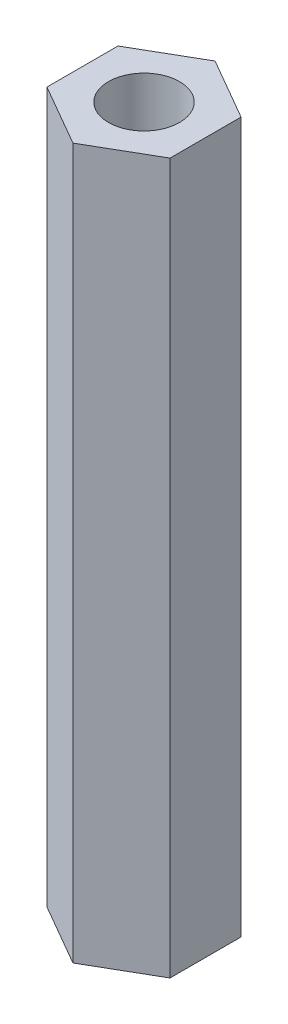
SolidWorks part; units mm, degrees
ref_plane "Front Plane" through (0, 0, 0) normal (0, 0, 1) x (1, 0, 0)
ref_plane "Top Plane" through (0, 0, 0) normal (0, 1, 0) x (1, 0, 0)
ref_plane "Right Plane" through (0, 0, 0) normal (1, 0, 0) x (0, 0, -1)
sketch "Sketch1" plane through (0, 0, 0) normal (0, 1, 0) x (1, 0, 0)
  line L0 (0, 0) -> (2.6, 0) construction
  line L1 (0, 3.0022) -> (-2.6, 1.5011)
  line L2 (-2.6, 1.5011) -> (-2.6, -1.5011)
  line L3 (-2.6, -1.5011) -> (0, -3.0022)
  line L4 (0, -3.0022) -> (2.6, -1.5011)
  line L5 (2.6, -1.5011) -> (2.6, 1.5011)
  line L6 (2.6, 1.5011) -> (0, 3.0022)
  circle A0 centre (0, 0) radius 1.5
  circle A1 centre (0, 0) radius 2.6 construction
  dimension "D1" = 3
  dimension "D2" = 2.6
extrude "Boss-Extrude2" add sketch "Sketch1" along normal blind 30
